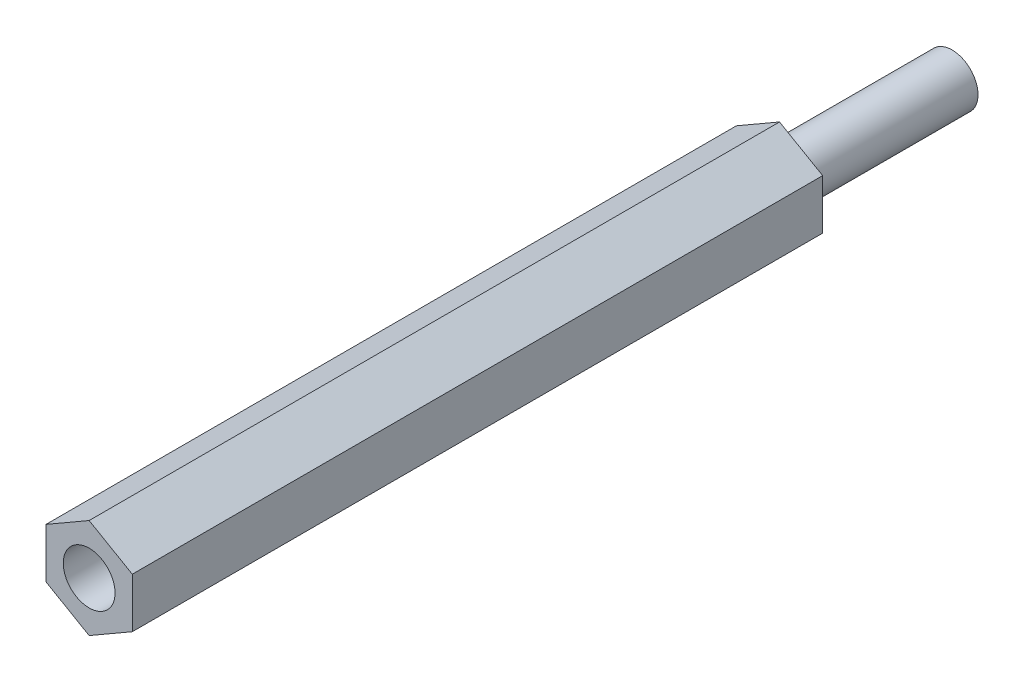
SolidWorks part; units mm, degrees
ref_plane "Plan de face" through (0, 0, 0) normal (0, 0, 1) x (1, 0, 0)
ref_plane "Plan de dessus" through (0, 0, 0) normal (0, 1, 0) x (1, 0, 0)
ref_plane "Plan de droite" through (0, 0, 0) normal (1, 0, 0) x (0, 0, -1)
sketch "Esquisse1" plane through (0, 0, 0) normal (0, 0, 1) x (1, 0, 0)
  line L1 (0, -2.8868) -> (2.5, -1.4434)
  line L2 (2.5, -1.4434) -> (2.5, 1.4434)
  line L3 (2.5, 1.4434) -> (0, 2.8868)
  line L4 (0, 2.8868) -> (-2.5, 1.4434)
  line L5 (-2.5, 1.4434) -> (-2.5, -1.4434)
  line L6 (-2.5, -1.4434) -> (0, -2.8868)
  circle A0 centre (0, 0) radius 2.5 construction
  circle A1 centre (0, 0) radius 1.5
  dimension "D1" = 3
  dimension "D2" = 5
extrude "Boss.-Extru.2" add sketch "Esquisse1" along normal blind 40 contours A1 | L1 L2 L3 L4 L5 L6
sketch "Esquisse3" plane through (0, 0, 0) normal (0, 0, -1) x (-1, 0, 0)
  circle A0 centre (0, 0) radius 1.5
extrude "Boss.-Extru.3" add sketch "Esquisse3" against normal blind 30 and the other way blind 10
